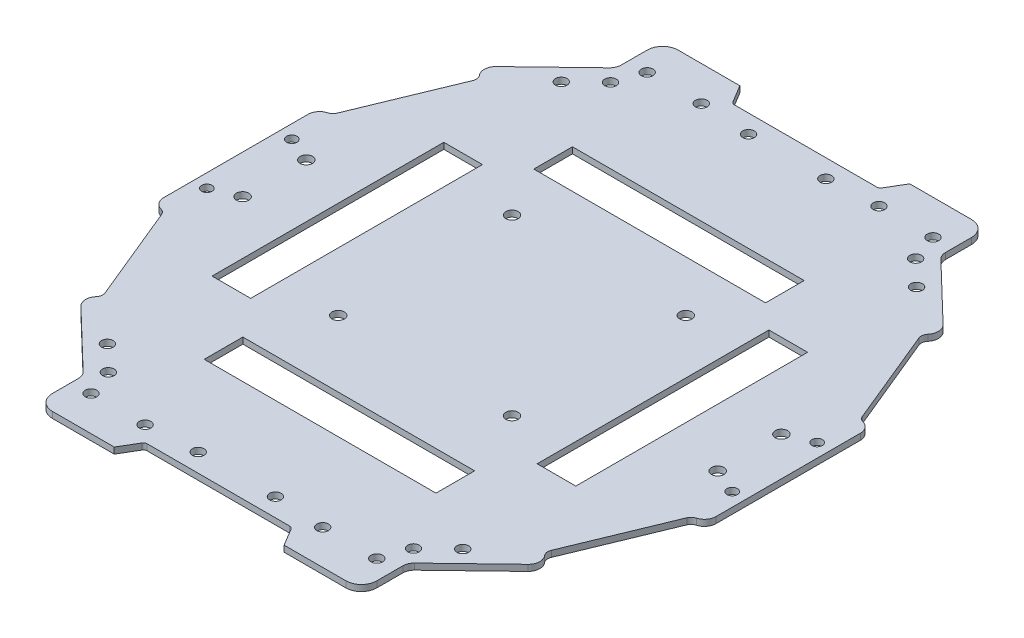
SolidWorks part; units mm, degrees
ref_plane "Front Plane" through (0, 0, 0) normal (0, 0, 1) x (1, 0, 0)
ref_plane "Top Plane" through (0, 0, 0) normal (0, 1, 0) x (1, 0, 0)
ref_plane "Right Plane" through (0, 0, 0) normal (1, 0, 0) x (0, 0, -1)
ref_plane "Plane1"
sketch "Sketch1" plane through (0, 0, 0) normal (0, 1, 0) x (-1, 0, 0)
  line L0 (59.7752, 259.0599) -> (56.7752, 264.0599)
  line L1 (56.7752, 264.0599) -> (36.7752, 264.0599)
  line L2 (36.7752, 264.0599) -> (36.7752, 252.0599)
  line L3 (36.7752, 252.0599) -> (18.7553, 234.7311)
  line L4 (18.7553, 234.7311) -> (21.5279, 231.8479)
  line L5 (21.5279, 231.8479) -> (10.2752, 204.5599)
  line L6 (10.2752, 204.5599) -> (7.2752, 204.5599)
  line L7 (7.2752, 204.5599) -> (7.2752, 183.0599)
  line L8 (7.2752, 183.0599) -> (7.2752, 161.5599)
  line L9 (7.2752, 161.5599) -> (10.2752, 161.5599)
  line L10 (10.2752, 161.5599) -> (21.5279, 134.2718)
  line L11 (21.5279, 134.2718) -> (18.7553, 131.3886)
  line L12 (18.7553, 131.3886) -> (36.7752, 114.0599)
  line L13 (36.7752, 114.0599) -> (36.7752, 102.0599)
  line L14 (36.7752, 102.0599) -> (56.7752, 102.0599)
  line L15 (56.7752, 102.0599) -> (59.7752, 107.0599)
  line L16 (59.7752, 107.0599) -> (78.7752, 107.0599)
  line L17 (78.7752, 107.0599) -> (97.7752, 107.0599)
  line L18 (97.7752, 107.0599) -> (100.7752, 102.0599)
  line L19 (100.7752, 102.0599) -> (120.7752, 102.0599)
  line L20 (120.7752, 102.0599) -> (120.7752, 114.0599)
  line L21 (120.7752, 114.0599) -> (138.795, 131.3886)
  line L22 (138.795, 131.3886) -> (136.0224, 134.2718)
  line L23 (136.0224, 134.2718) -> (147.2752, 161.5599)
  line L24 (147.2752, 161.5599) -> (150.2752, 161.5599)
  line L25 (150.2752, 161.5599) -> (150.2752, 183.0599)
  line L26 (150.2752, 183.0599) -> (150.2752, 204.5599)
  line L27 (150.2752, 204.5599) -> (147.2752, 204.5599)
  line L28 (147.2752, 204.5599) -> (136.0224, 231.8479)
  line L29 (136.0224, 231.8479) -> (138.795, 234.7311)
  line L30 (138.795, 234.7311) -> (120.7752, 252.0599)
  line L31 (120.7752, 252.0599) -> (120.7752, 264.0599)
  line L32 (120.7752, 264.0599) -> (100.7752, 264.0599)
  line L33 (100.7752, 264.0599) -> (97.7752, 259.0599)
  line L34 (97.7752, 259.0599) -> (78.7752, 259.0599)
  line L35 (78.7752, 259.0599) -> (59.7752, 259.0599)
  line L36 (78.7752, 259.0599) -> (78.7752, 107.0599) construction
  line L38 (150.2752, 183.0599) -> (7.2752, 183.0599) construction
  line L62 (63.7752, 136.4301) -> (93.7752, 151.9284) construction
  line L85 (91.8838, 199.6325) -> (91.9874, 199.5289)
  line L87 (95.3777, 196.1387) -> (95.4193, 196.097)
  circle A0 centre (55.7752, 111.0599) radius 1.5
  circle A1 centre (39.2752, 118.0599) radius 1.5
  circle A2 centre (56.2752, 205.5599) radius 1.6
  circle A4 centre (17.2752, 174.8099) radius 1.6
  circle A10 centre (101.2752, 205.5599) radius 1.6
  circle A11 centre (56.2752, 160.5599) radius 1.6
  circle A12 centre (101.2752, 160.5599) radius 1.6
  circle A22 centre (41.7752, 255.0599) radius 1.5
  circle A23 centre (39.2752, 248.0599) radius 1.5
  circle A24 centre (10.7752, 194.0599) radius 1.35
  circle A25 centre (88.7752, 111.8099) radius 1.5
  circle A27 centre (115.7752, 111.0599) radius 1.5
  circle A28 centre (118.2752, 118.0599) radius 1.5
  circle A29 centre (140.2752, 174.8099) radius 1.6
  circle A30 centre (115.7752, 255.0599) radius 1.5
  circle A31 centre (88.7752, 254.3099) radius 1.5
  circle A32 centre (140.2752, 191.3099) radius 1.6
  circle A33 centre (146.7752, 194.0599) radius 1.35
  circle A53 centre (101.7752, 255.0599) radius 1.5
  circle A54 centre (118.2752, 248.0599) radius 1.5
  circle A55 centre (146.7752, 172.0599) radius 1.35
  circle A57 centre (101.7752, 111.0599) radius 1.5
  circle A69 centre (17.2752, 191.3099) radius 1.6
  circle A71 centre (55.7752, 255.0599) radius 1.5
  circle A73 centre (68.7752, 254.3099) radius 1.5
  circle A74 centre (10.7752, 172.0599) radius 1.35
  circle A76 centre (68.7752, 111.8099) radius 1.5
  circle A77 centre (41.7752, 111.0599) radius 1.5
  circle A82 centre (32.7752, 124.3099) radius 1.5
  circle A86 centre (124.7752, 241.8099) radius 1.5
  circle A87 centre (32.7752, 241.8099) radius 1.5
  circle A91 centre (124.7752, 124.3099) radius 1.5
  point P41 (150.2752, 193.8099)
  point P62 (124.7752, 183.0599)
  point P67 (40.2985, 183.0599)
  dimension "D1" = 143
  dimension "D2" = 162
  dimension "D3" = 22.5
  dimension "D4" = 22.5
extrude "Extrusion1" add sketch "Sketch1" along normal blind 1.6
fillet "Fillet1" radius 1 4 edges at (-97.7752, 0.8, 107.0599) (-59.7752, 0.8, 107.0599) (-59.7752, 0.8, 259.0599) (-97.7752, 0.8, 259.0599)
fillet "Fillet2" radius 4 4 edges at (-120.7752, 0.8, 102.0599) (-36.7752, 0.8, 102.0599) (-120.7752, 0.8, 264.0599) (-36.7752, 0.8, 264.0599)
fillet "Fillet3" radius 3 4 edges at (-120.7752, 0.8, 114.0599) (-36.7752, 0.8, 114.0599) (-36.7752, 0.8, 252.0599) (-120.7752, 0.8, 252.0599)
fillet "Fillet4" radius 3 1 edges at (-138.795, 0.8, 234.7311)
fillet "Fillet5" radius 2 1 edges at (-136.0224, 0.8, 231.8479)
fillet "Fillet6" radius 2 1 edges at (-21.5279, 0.8, 231.8479)
fillet "Fillet7" radius 3 1 edges at (-18.7553, 0.8, 234.7311)
fillet "Fillet8" radius 3 2 edges at (-138.795, 0.8, 131.3886) (-18.7553, 0.8, 131.3886)
fillet "Fillet9" radius 2 2 edges at (-21.5279, 0.8, 134.2718) (-136.0224, 0.8, 134.2718)
fillet "Fillet10" radius 2 4 edges at (-10.2752, 0.8, 161.5599) (-10.2752, 0.8, 204.5599) (-147.2752, 0.8, 204.5599) (-147.2752, 0.8, 161.5599)
fillet "Fillet11" radius 3 4 edges at (-150.2752, 0.8, 161.5599) (-150.2752, 0.8, 204.5599) (-7.2752, 0.8, 204.5599) (-7.2752, 0.8, 161.5599)
sketch "Sketch2" plane through (0, 1.6, 0) normal (0, 1, 0) x (1, 0, 0)
  line L0 (-97.209, -259.0599) -> (-60.3413, -259.0599) construction
  line L1 (-48.7752, -232.7401) -> (-108.7752, -232.7401)
  line L2 (-48.7752, -232.7401) -> (-48.7752, -222.7401)
  line L3 (-48.7752, -222.7401) -> (-108.7752, -222.7401)
  line L4 (-108.7752, -232.7401) -> (-108.7752, -222.7401)
  line L5 (-48.7752, -232.7401) -> (-108.7752, -222.7401) construction
  line L6 (-48.7752, -222.7401) -> (-108.7752, -232.7401) construction
  line L7 (-116.4278, -213.0599) -> (-126.4278, -213.0599)
  line L8 (-116.4278, -213.0599) -> (-116.4278, -153.0599)
  line L9 (-116.4278, -153.0599) -> (-126.4278, -153.0599)
  line L10 (-126.4278, -213.0599) -> (-126.4278, -153.0599)
  line L11 (-116.4278, -213.0599) -> (-126.4278, -153.0599) construction
  line L12 (-116.4278, -153.0599) -> (-126.4278, -213.0599) construction
  line L13 (-32.2554, -213.0599) -> (-42.2554, -213.0599)
  line L14 (-32.2554, -213.0599) -> (-32.2554, -153.0599)
  line L15 (-32.2554, -153.0599) -> (-42.2554, -153.0599)
  line L16 (-42.2554, -213.0599) -> (-42.2554, -153.0599)
  line L17 (-32.2554, -213.0599) -> (-42.2554, -153.0599) construction
  line L18 (-32.2554, -153.0599) -> (-42.2554, -213.0599) construction
  line L19 (-48.7752, -147.4174) -> (-108.7752, -147.4174)
  line L20 (-48.7752, -147.4174) -> (-48.7752, -137.4174)
  line L21 (-48.7752, -137.4174) -> (-108.7752, -137.4174)
  line L22 (-108.7752, -147.4174) -> (-108.7752, -137.4174)
  line L23 (-48.7752, -147.4174) -> (-108.7752, -137.4174) construction
  line L24 (-48.7752, -137.4174) -> (-108.7752, -147.4174) construction
  line L25 (-78.7752, -259.0599) -> (-78.7752, -107.0599) construction
  line L26 (-60.3413, -107.0599) -> (-97.209, -107.0599) construction
  line L27 (-7.2752, -183.0599) -> (-150.2752, -183.0599) construction
  line L28 (-7.2752, -201.7424) -> (-7.2752, -164.3774) construction
  line L29 (-150.2752, -164.3774) -> (-150.2752, -201.7424) construction
  point P0 (-78.7752, -227.7401)
  point P5 (-121.4278, -183.0599)
  point P10 (-37.2554, -183.0599)
  point P15 (-78.7752, -142.4174)
  point P20 (0, 0)
  point P27 (0, 0)
extrude "Cut-Extrude1" cut sketch "Sketch2" against normal blind 10
